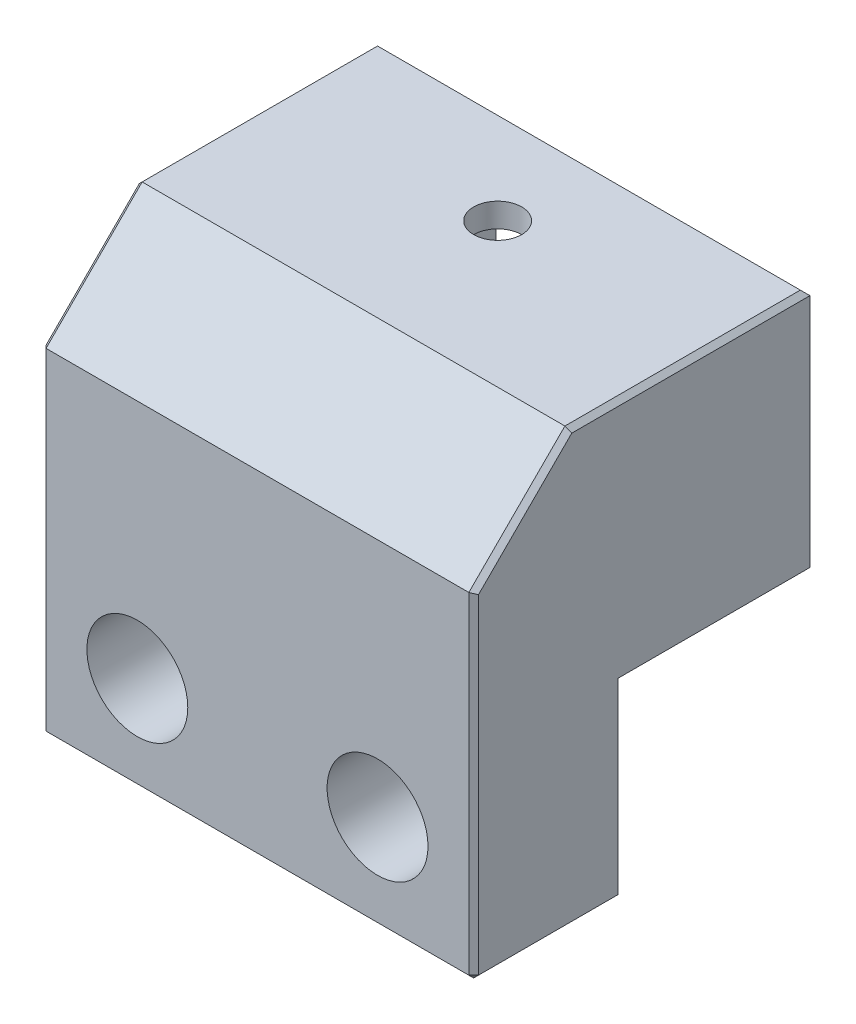
SolidWorks part; units mm, degrees
ref_plane "Front Plane" through (0, 0, 0) normal (0, 0, 1) x (1, 0, 0)
ref_plane "Top Plane" through (0, 0, 0) normal (0, 1, 0) x (1, 0, 0)
ref_plane "Right Plane" through (0, 0, 0) normal (1, 0, 0) x (0, 0, -1)
sketch "Sketch1" plane through (0, 0, 0) normal (0, 1, 0) x (1, 0, 0)
  line L0 (0, 0) -> (-22.5, 0) construction
  line L2 (-22.5, 10) -> (22.5, 10)
  line L3 (-22.5, 10) -> (-22.5, -10)
  line L4 (-22.5, -10) -> (22.5, -10)
  line L5 (22.5, 10) -> (22.5, -10)
  line L6 (-22.5, 10) -> (22.5, -10) construction
  line L7 (-22.5, -10) -> (22.5, 10) construction
  circle A0 centre (0, 0) radius 2.5
  point P3 (0, 0)
  dimension "D1" = 5
  dimension "D2" = 20
  dimension "D3" = 22.5
extrude "Boss-Extrude1" add sketch "Sketch1" along normal blind 25
sketch "Sketch9" plane through (0, 0, 10) normal (0, 0, 1) x (1, 0, 0)
  line L1 (-22.5, 25) -> (22.5, 25)
  line L2 (-22.5, 25) -> (-22.5, -20)
  line L3 (-22.5, -20) -> (22.5, -20)
  line L4 (22.5, 25) -> (22.5, -20)
  line L5 (22.5, 25) -> (22.5, 0) construction
  line L6 (-22.5, 0) -> (22.5, 0) construction
  dimension "D1" = 20
extrude "Boss-Extrude4" add sketch "Sketch9" along normal blind 15
sketch "Sketch10" plane through (0, 25, 0) normal (0, 1, 0) x (1, 0, 0)
  line L0 (10.16, 0) -> (10.16, 10)
  line L1 (22.5, 10) -> (-22.5, 10) construction
  line L2 (10.16, 10) -> (-10.16, 10)
  line L3 (-10.16, 10) -> (-10.16, 0)
  arc A0 (10.16, 0) -> (-10.16, 0) centre (0, 0) cw
  dimension "D1" = 10.16
extrude "Cut-Extrude2" cut sketch "Sketch10" against normal blind 19.5 from offset 2.5 offset against normal yes
chamfer "Chamfer1" distance 10 angle 45 1 edges at (0, 25, 25)
sketch "Sketch11" plane through (0, 0, 25) normal (0, 0, 1) x (1, 0, 0)
  line L0 (-22.5, -10) -> (22.5, -10) construction
  line L1 (22.5, -20) -> (22.5, 15) construction
  line L2 (-22.5, 15) -> (-22.5, -20) construction
  line L3 (-22.5, -20) -> (22.5, -20) construction
  circle A0 centre (-12.5, -10) radius 10
  circle A1 centre (12.5, -10) radius 10
  dimension "D2" = 20
  dimension "D1" = 10
hole_wizard "CBORE for M5 SBHCS1" positions "Sketch12" profile "Sketch13" counterbore size "M5" standard "ANSI Metric" end condition through all
sketch "Sketch12" plane through (0, 0, 25) normal (0, 0, 1) x (1, 0, 0)
  point P0 (-12.5, -10)
  point P3 (12.5, -10)
sketch "Sketch13" plane through (-12.5, -10, 25) normal (1, 0, 0) x (0, -1, 0)
  line L0 (0, 0) -> (0, 35)
  line L1 (0, 35) -> (2.75, 35)
  line L3 (2.75, 35) -> (2.75, 9.75)
  line L4 (2.75, 9.75) -> (5.25, 9.75)
  line L5 (5.25, 9.75) -> (5.25, 0)
  line L7 (5.25, 0) -> (0, 0)
  line L11 (0, -6.35) -> (0, 107.95) construction
  dimension "Thru Hole Dia." = 5.5
  dimension "Thru Hole Depth" = 35
  dimension "C'Bore Dia." = 10.5
  dimension "C'Bore Depth" = 9.75
chamfer "Chamfer2" distance 0.5 angle 45 10 edges at (22.5, -20, 17.5) (-22.5, -20, 17.5) (22.5, 20, 20) (22.5, 25, 2.5) (0, 25, -10) (-22.5, 25, 2.5) (-22.5, 20, 20) (22.5, -2.5, 25) (0, -20, 25) (-22.5, -2.5, 25)
